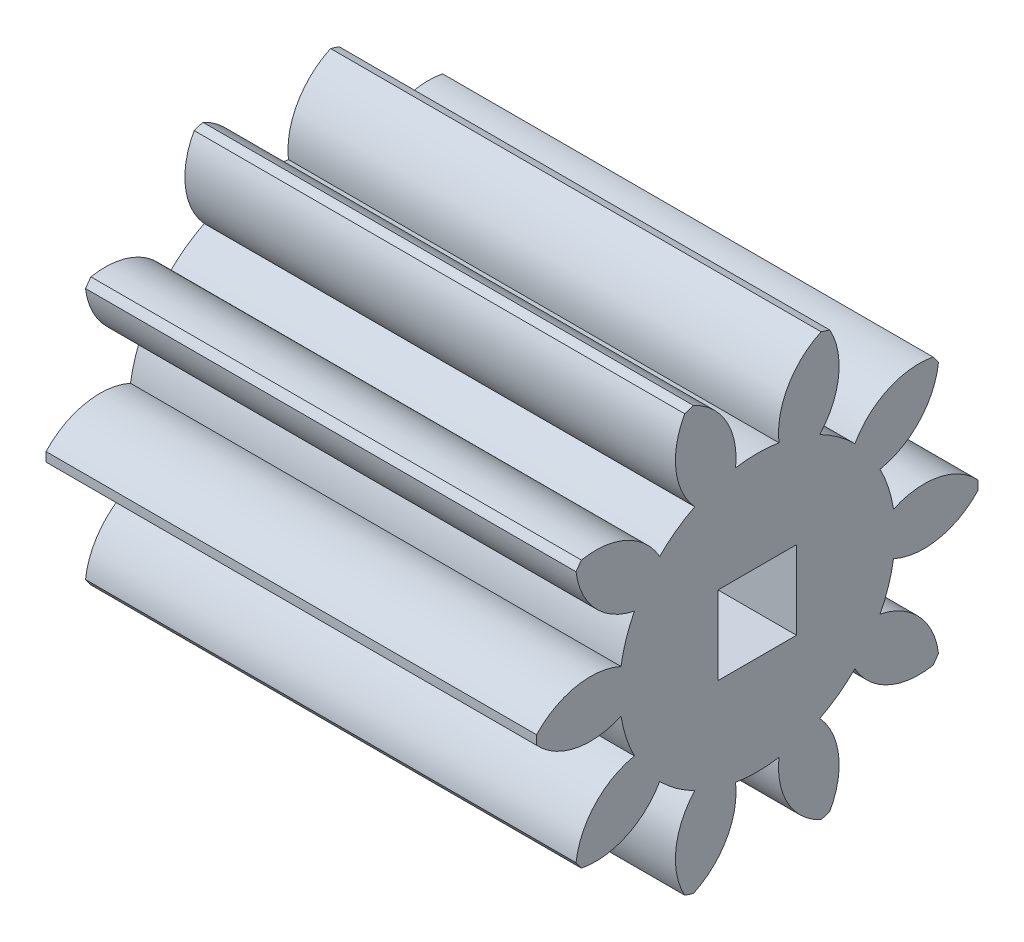
SolidWorks part; units mm, degrees
ref_plane "Plane1" through (0, 0, 0) normal (0, 0, 1) x (1, 0, 0)
ref_plane "Plane2" through (0, 0, 0) normal (0, 1, 0) x (1, 0, 0)
ref_plane "Plane3" through (0, 0, 0) normal (1, 0, 0) x (0, 0, -1)
other "Configuration Table"
sketch "HoldingSke" plane through (0, 0, 0) normal (0, 1, 0) x (1, 0, 0)
  line L0 (0, 0) -> (0.6565, -0.1158)
  line L1 (-15, 0) -> (100, 0) construction
  line L2 (0, 0) -> (-2.1039, 2.3779)
  line L3 (0, 0) -> (-11.863, 4.5341)
  line L4 (0, 0) -> (8.5048, 1.4996)
  line L5 (0, 0) -> (-46.8476, -17.4728)
  line L6 (0, 0) -> (-16.5793, -11.1861)
  line L7 (-2.1039, 2.3779) -> (8.6586, 51.2059)
  line L8 (-76.2, 54.61) -> (-75.7, 54.61)
  line L9 (-71.009, 38.7566) -> (-53.1078, 45.2721)
  line L10 (-76.2, 71.12) -> (104.1128, 71.12)
  line L11 (0, 0) -> (-20, 0)
  line L12 (-76.2, 101.6) -> (-76.147, 101.6)
  line L13 (24.9733, 27.94) -> (52.9518, 28.4284)
  line L14 (24.9733, 27.94) -> (24.9743, 27.94)
  line L15 (24.9733, 27.94) -> (100.4006, 29.5858)
  line L16 (-63.627, -1.5) -> (-12.827, -1.5)
  circle A0 centre (0, 0) radius 1.5
  circle A1 centre (0, 0) radius 5.624
  circle A2 centre (0, 0) radius 37.5
  circle A3 centre (0, 0) radius 1.5
  dimension "MHD" = 11.248
  dimension "Hub_dia" = 75
  dimension "Bore" = 3
  dimension "MBD" = 3
  dimension "Num_teeth" = 10
  dimension "Pitch" = 0.6667
  dimension "Overall_len" = 50
  dimension "Show_teeth" = 10
  dimension "Thickness" = 20
  dimension "OAL" = 50.0001
  dimension "T_dim" = 0.5
  dimension "Ap" = 20
  dimension "H" = 19.05
  dimension "Pitch_radius" = 180.3128
  dimension "Width" = 20
  dimension "Backlash" = 0.053
  dimension "Addendum_fac" = 1
  dimension "Dedendum_fac" = 1.25
  dimension "Clearance_fac" = 0.25
  dimension "Dedendum_add" = 0.001
  dimension "Module" = 1.5
sketch "BasProSke" plane through (0, 0, 0) normal (0, 1, 0) x (1, 0, 0)
  line L0 (-10, 0) -> (60, 0) construction
  line L1 (0, 0) -> (0, 9)
  line L2 (0, 0) -> (20, 0)
  line L3 (20, 0) -> (20, 9)
  line L4 (20, 9) -> (0, 9)
  dimension "Thickness" = 20
  dimension "Diameter" = 18
revolve "Base-Revolve" add sketch "BasProSke" angle 360 about L0
sketch "TooCutSke" plane through (0, 0, 0) normal (1, 0, 0) x (0, 0, -1)
  line L1 (0, 0) -> (0, 107) construction
  line L2 (0, 0) -> (-1.2658, 7.3924) construction
  line L3 (0, 0) -> (-4.5869, 14.117) construction
  line L4 (-1.2658, 7.3924) -> (-2.2934, 7.0585) construction
  arc A0 (0.8839, 5.5541) -> (-0.8839, 5.5541) centre (0, 0) ccw
  arc A1 (2.6378, 8.6313) -> (-2.6378, 8.6313) centre (0, 0) ccw
  circle A2 centre (0, 0) radius 7.5 construction
  circle A3 centre (0, 0) radius 7.0477 construction
  arc A4 (-0.8839, 5.5541) -> (-2.6378, 8.6313) centre (-3.8646, 5.8936) ccw
  arc A5 (2.6378, 8.6313) -> (0.8839, 5.5541) centre (3.8646, 5.8936) ccw
  dimension "Root_dia" = 11.248
  dimension "Overcut_dia" = 18.0508
  dimension "Pitch_dia" = 15
  dimension "Base_dia" = 14.0954
  dimension "Flank_rad" = 3
  dimension "Half_ang" = 18
  dimension "Half_CT" = 1.0805
extrude "ToothCut" cut sketch "TooCutSke" along normal through all
fillet "Breaks" [suppressed] radius 0.03
fillet "RootFillets" [suppressed] radius 0.376
pattern_circular "TeethCuts" count 10 every 36 about axis through (-10, 0, 0) along (1, 0, 0) of "ToothCut", "RootFillets", "Breaks"
sketch "HubNeaOneSke" plane through (0, 0, 0) normal (-1, 0, 0) x (0, 0, 1)
  circle A0 centre (0, 0) radius 5.624
  dimension "Diameter" = 11.248
extrude "HubNearOne" [suppressed] add sketch "HubNeaOneSke" along normal blind 30.0001
sketch "HubNeaBotSke" plane through (0, 0, 0) normal (-1, 0, 0) x (0, 0, 1)
  circle A0 centre (0, 0) radius 5.624
  dimension "Diameter" = 11.248
extrude "HubNearBoth" [suppressed] add sketch "HubNeaBotSke" along normal blind 15
ref_plane "FarPln" through (20, 0, 0) normal (1, 0, 0) x (0, 0, -1)
sketch "HubFarSke" plane through (20, 0, 0) normal (1, 0, 0) x (0, 0, -1)
  circle A0 centre (0, 0) radius 5.624
  dimension "Diameter" = 11.248
extrude "HubFar" [suppressed] add sketch "HubFarSke" along normal blind 15
sketch "BorSke" plane through (0, 0, 0) normal (1, 0, 0) x (0, 0, -1)
  circle A0 centre (0, 0) radius 1.5
  dimension "Diameter" = 3
extrude "Bore" cut sketch "BorSke" along normal mid plane 100.0001
sketch "KeySke" plane through (0, 0, 0) normal (1, 0, 0) x (0, 0, -1)
  line L0 (-0.6, 0) -> (-0.6, 2)
  line L1 (-0.6, 2) -> (0.6, 2)
  line L2 (0.6, 2) -> (0.6, 0)
  line L3 (0, 0) -> (0, 34) construction
  line L4 (-0.6, 0) -> (0.6, 0)
  dimension "Offset" = 2
  dimension "Width" = 1.2
extrude "Keyway" [suppressed] cut sketch "KeySke" along normal mid plane 100.0001
pattern_circular "Keyway2" [suppressed] count 2 every 90 about axis through (-10, 0, 0) along (1, 0, 0)
sketch "Sketch1" plane through (20, 0, 0) normal (1, 0, 0) x (0, 0, -1)
  line L1 (-1.6, -1.6) -> (1.6, -1.6)
  line L2 (-1.6, -1.6) -> (-1.6, 1.6)
  line L3 (-1.6, 1.6) -> (1.6, 1.6)
  line L4 (1.6, -1.6) -> (1.6, 1.6)
  line L5 (-1.6, -1.6) -> (1.6, 1.6) construction
  line L6 (-1.6, 1.6) -> (1.6, -1.6) construction
  point P0 (0, 0)
  dimension "D1" = 3.2
  dimension "D2" = 3.2
extrude "Cut-Extrude1" cut sketch "Sketch1" against normal blind 10
equation "' \"Module@HoldingSke\" = 6.35"
equation "' \"Num_teeth@HoldingSke\" = 12"
equation "' \"Ap@HoldingSke\" =  20"
equation "' \"Ap@HoldingSke\" = 20"
equation "' \"Width@HoldingSke\" = 0.5 * 25.4"
equation "' \"Hub_dia@HoldingSke\"= 1 * 25.4"
equation "' \"Hub_dia@HoldingSke\" = 1 * 25.4"
equation "' \"Overall_len@HoldingSke\" = 1.0 * 25.4"
equation "' \"Bore@HoldingSke\" = 0.75 * 25.4"
equation "' \"T_dim@HoldingSke\" = 0.1 * 25.4"
equation "' \"Width@KeySke\" = 0.25 * 25.4"
equation "' \"Show_teeth@HoldingSke\" = 13"
equation "' \"Backlash@HoldingSke\" = 0.009 * 25.4"
equation "' \"Addendum_fac@HoldingSke\" = 1.0"
equation "' \"Dedendum_fac@HoldingSke\" = 1.25"
equation "' \"Dedendum_add@HoldingSke\" = 0.00005 * 25.4"
equation "' \"Clearance_fac@HoldingSke\" = 0.25"
equation "\"Pitch@HoldingSke\" = 1 / \"Module@HoldingSke\""
equation "\"Overcut_dia@TooCutSke\" = (\"Num_teeth@HoldingSke\" + 2 * \"Addendum_fac@HoldingSke\") / \"Pitch@HoldingSke\" + 0.002 * 25.4"
equation "\"Pitch_dia@TooCutSke\" = \"Num_teeth@HoldingSke\" / \"Pitch@HoldingSke\""
equation "\"Base_dia@TooCutSke\" = \"Num_teeth@HoldingSke\" / \"Pitch@HoldingSke\" * cos((\"Ap@HoldingSke\"  * 3.14159265 / 180))"
equation "\"Root_dia@TooCutSke\" = (\"Num_teeth@HoldingSke\" + 2) / \"Pitch@HoldingSke\" - 2 * (\"Addendum_fac@HoldingSke\" + \"Dedendum_fac@HoldingSke\") / \"Pitch@HoldingSke\" - \"Dedendum_add@HoldingSke\" * 2"
equation "\"Half_ang@TooCutSke\" = 180 / \"Num_teeth@HoldingSke\""
equation "\"Half_CT@TooCutSke\" = \"Num_teeth@HoldingSke\" / \"Pitch@HoldingSke\" * sin((3.14159265 / 2 / \"Num_teeth@HoldingSke\")) / 2 - 7 * \"Backlash@HoldingSke\" / 4"
equation "\"Flank_rad@TooCutSke\" = \"Num_teeth@HoldingSke\" / \"Pitch@HoldingSke\" / 5"
equation "\"Radius@RootFillets\" = \"Clearance_fac@HoldingSke\" / \"Pitch@HoldingSke\" + \"Dedendum_add@HoldingSke\""
equation "\"Break_rad@Breaks\" = 0.02 / \"Pitch@HoldingSke\""
equation "\"Thickness@HoldingSke\" = \"Width@HoldingSke\""
equation "\"OAL@HoldingSke\" = \"Thickness@HoldingSke\""
equation "\"MHD@HoldingSke\" = (\"Num_teeth@HoldingSke\" + 2) / \"Pitch@HoldingSke\" - 2 * (\"Addendum_fac@HoldingSke\" + \"Dedendum_fac@HoldingSke\")  / \"Pitch@HoldingSke\" - \"Dedendum_add@HoldingSke\" * 2"
equation "\"MBD@HoldingSke\" = (\"Num_teeth@HoldingSke\" + 2) / \"Pitch@HoldingSke\" - 2 * (\"Addendum_fac@HoldingSke\" + \"Dedendum_fac@HoldingSke\")  / \"Pitch@HoldingSke\" - \"Dedendum_add@HoldingSke\" * 2 - 0.002 * 25.4"
equation "\"MHD@HoldingSke\" = ((sgn( \"MHD@HoldingSke\" - \"Hub_dia@HoldingSke\" )-1)*( \"MHD@HoldingSke\" - \"Hub_dia@HoldingSke\" ))/-2+ \"Hub_dia@HoldingSke\""
equation "\"MBD@HoldingSke\" = ((sgn( \"MBD@HoldingSke\" - \"Bore@HoldingSke\" )-1)*( \"MBD@HoldingSke\" - \"Bore@HoldingSke\" ))/-2+ \"Bore@HoldingSke\""
equation "\"OAL@HoldingSke\" = ((sgn( \"OAL@HoldingSke\" - \"Overall_len@HoldingSke\" )+1)*( \"OAL@HoldingSke\" - \"Overall_len@HoldingSke\" ))/2 + \"Overall_len@HoldingSke\" + 0.000002 * 25.4"
equation "\"Num_teeth@TeethCuts\" = int( \"Show_teeth@HoldingSke\" ) + 1"
equation "\"Num_teeth@TeethCuts\" = ((sgn( \"Num_teeth@TeethCuts\" - \"Num_teeth@HoldingSke\" )-1)*( \"Num_teeth@TeethCuts\" - \"Num_teeth@HoldingSke\" ))/-2+ \"Num_teeth@HoldingSke\""
equation "\"Num_teeth@TeethCuts\" = ((sgn( \"Num_teeth@TeethCuts\" - 2.0)+1)*( \"Num_teeth@TeethCuts\" - 2.0))/2 +2.0"
equation "\"Angle@TeethCuts\" = 360.0 / \"Num_teeth@HoldingSke\""
equation "\"Diameter@BasProSke\" = (\"Num_teeth@HoldingSke\" + 2 * \"Addendum_fac@HoldingSke\") / \"Pitch@HoldingSke\""
equation "\"Thickness@BasProSke\"  = \"Thickness@HoldingSke\""
equation "' \"Fillet_rad@BasProSke\" =  \"Thickness@HoldingSke\" * 0.05"
equation "' \"Fillet_rad@BasProSke\" = \"Thickness@HoldingSke\" * 0.05"
equation "\"MHD@HoldingSke\" = ((sgn( \"MHD@HoldingSke\" - \"Root_dia@TooCutSke\" )-1)*( \"MHD@HoldingSke\" - \"Root_dia@TooCutSke\" ))/-2+ \"Root_dia@TooCutSke\""
equation "\"Diameter@HubNeaOneSke\" = \"MHD@HoldingSke\""
equation "\"Length@HubNearOne\" = \"OAL@HoldingSke\" - \"Thickness@BasProSke\""
equation "\"Diameter@HubNeaBotSke\" = \"MHD@HoldingSke\""
equation "\"Length@HubNearBoth\" = ( \"OAL@HoldingSke\" - \"Thickness@BasProSke\" ) / 2.0"
equation "\"Thickness@FarPln\" = \"Thickness@BasProSke\""
equation "\"Diameter@HubFarSke\" = \"MHD@HoldingSke\""
equation "\"Length@HubFar\" = ( \"OAL@HoldingSke\" - \"Thickness@BasProSke\" ) / 2.0"
equation "\"Diameter@BorSke\" = \"MBD@HoldingSke\""
equation "\"D1@Bore\" = \"OAL@HoldingSke\" * 2.0"
equation "\"D1@Keyway\" = \"OAL@HoldingSke\" * 2.0"
equation "\"Offset@KeySke\" = \"T_dim@HoldingSke\" + \"MBD@HoldingSke\" / 2.0"
